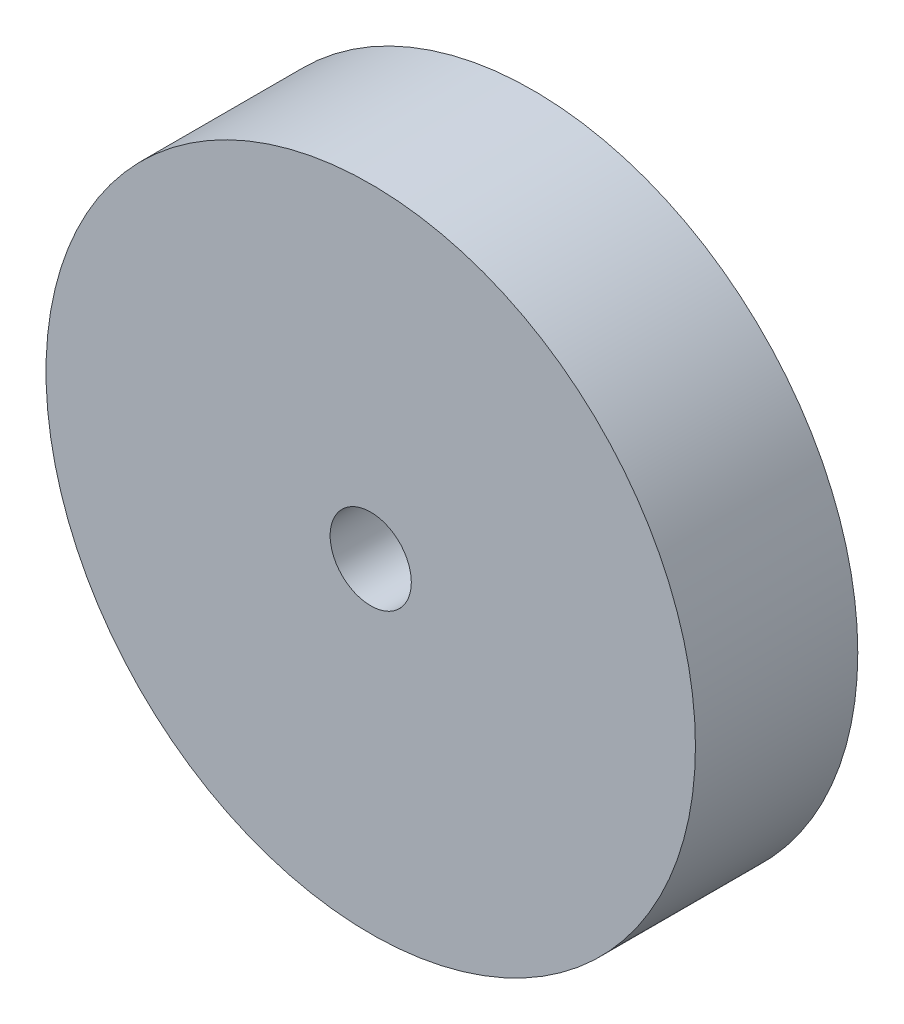
SolidWorks part; units mm, degrees
material "PP Copolymer"
ref_plane "Front Plane" through (0, 0, 0) normal (0, 0, 1) x (1, 0, 0)
ref_plane "Top Plane" through (0, 0, 0) normal (0, 1, 0) x (1, 0, 0)
ref_plane "Right Plane" through (0, 0, 0) normal (1, 0, 0) x (0, 0, -1)
sketch "Sketch1" plane through (0, 0, 0) normal (0, 0, 1) x (1, 0, 0)
  circle A0 centre (0, 0) radius 50.8
  circle A1 centre (0, 0) radius 6.35
  dimension "D1" = 101.6
  dimension "D2" = 12.7
extrude "Boss-Extrude1" add sketch "Sketch1" against normal mid plane 25.4
sketch "Sketch2" plane through (0, 0, 12.7) normal (0, 0, 1) x (1, 0, 0)
  circle A0 centre (-33.3744, -7.8247) radius 9.1252
